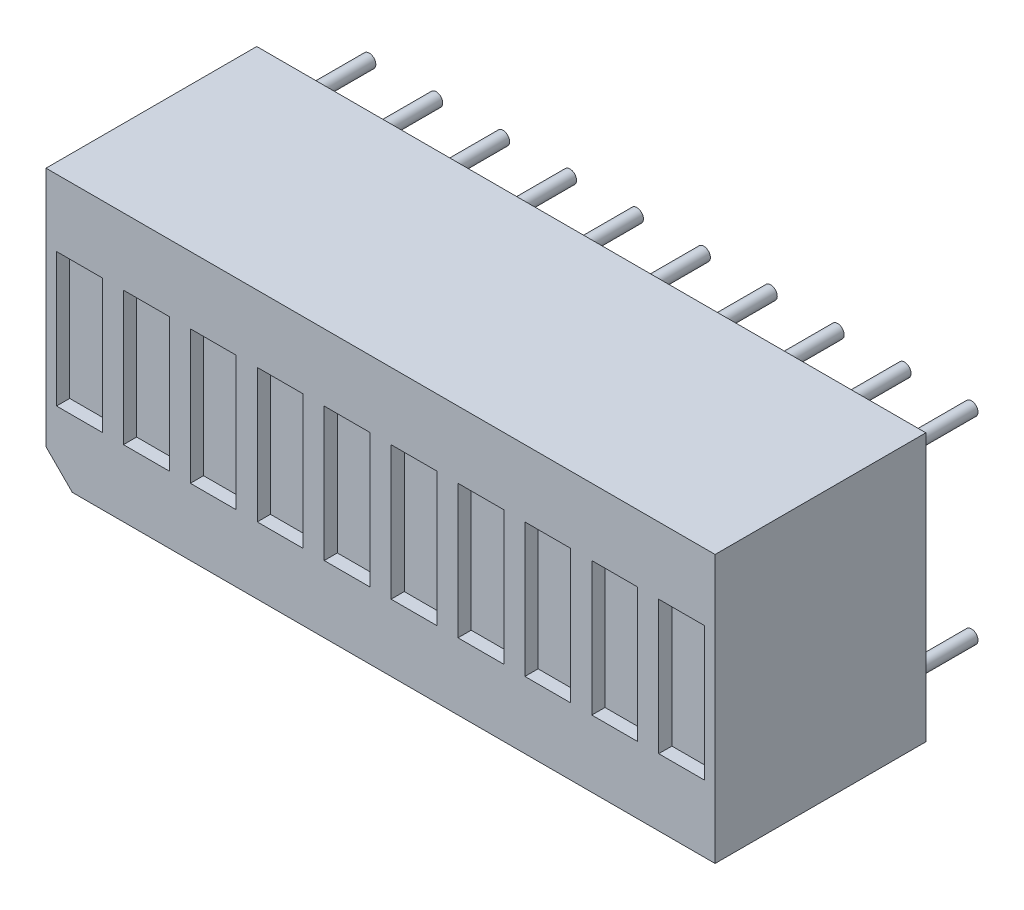
SolidWorks part; units mm, degrees
ref_plane "Alzado" through (0, 0, 0) normal (0, 0, 1) x (1, 0, 0)
ref_plane "Planta" through (0, 0, 0) normal (0, 1, 0) x (1, 0, 0)
ref_plane "Vista lateral" through (0, 0, 0) normal (1, 0, 0) x (0, 0, -1)
sketch "Croquis1" plane through (0, 0, 0) normal (0, 0, 1) x (1, 0, 0)
  line L0 (-11.7, -5.08) -> (-12.7, -4.08)
  line L1 (12.7, -5.08) -> (-11.7, -5.08)
  line L2 (12.7, -5.08) -> (12.7, 5.08)
  line L3 (12.7, 5.08) -> (-12.7, 5.08)
  line L4 (-12.7, -4.08) -> (-12.7, 5.08)
  line L5 (12.7, -5.08) -> (-12.7, 5.08) construction
  line L6 (12.7, 5.08) -> (-12.7, -5.08) construction
  point P0 (0, 0)
  dimension "D1" = 10.16
  dimension "D2" = 25.4
  dimension "D5" = 1
extrude "Saliente-Extruir1" add sketch "Croquis1" along normal blind 8
sketch "Croquis2" plane through (0, 0, 0) normal (0, 0, -1) x (-1, 0, 0)
  line L0 (0, 0) -> (-12.7, 0) construction
  line L1 (-12.7, -5.08) -> (-12.7, 5.08) construction
  line L3 (-12.7, 5.08) -> (12.7, 5.08) construction
  line L4 (0, 5.08) -> (0, 0) construction
  point P5 (-11.43, 3.75)
  point P9 (-8.89, 3.75)
  point P10 (-6.35, 3.75)
  point P11 (-1.27, 3.75)
  point P12 (-3.81, 3.75)
  dimension "D1" = 1.27
  dimension "D2" = 3.75
  dimension "D3" = 2.54
  dimension "D4" = 2.54
  dimension "D5" = 2.54
  dimension "D6" = 2.54
sketch "Croquis3" plane through (0, 0, 0) normal (0, 0, -1) x (-1, 0, 0)
  circle A0 centre (-11.43, 3.75) radius 0.25
  circle A1 centre (-8.89, 3.75) radius 0.25
  circle A2 centre (-6.35, 3.75) radius 0.25
  circle A3 centre (-3.81, 3.75) radius 0.25
  circle A4 centre (-1.27, 3.75) radius 0.25
  dimension "D1" = 0.5
extrude "Saliente-Extruir2" add sketch "Croquis3" along normal blind 3
pattern_linear "MatrizL1" count 2 spacing 12.7 along (-1, 0, 0) count 2 spacing 7.5 along (0, -1, 0) of "Saliente-Extruir2"
sketch "Croquis4" plane through (0, 0, 8) normal (0, 0, 1) x (1, 0, 0)
  line L0 (0, 0) -> (12.7, 0) construction
  line L1 (12.3, -2.54) -> (10.56, -2.54)
  line L2 (12.3, -2.54) -> (12.3, 2.54)
  line L3 (12.3, 2.54) -> (10.56, 2.54)
  line L4 (10.56, -2.54) -> (10.56, 2.54)
  line L5 (12.3, -2.54) -> (10.56, 2.54) construction
  line L6 (12.3, 2.54) -> (10.56, -2.54) construction
  line L7 (11.43, 0) -> (11.43, 3.75) construction
  point P0 (11.43, 0)
  dimension "D1" = 5.08
  dimension "D2" = 1.74
extrude "Cortar-Extruir1" cut sketch "Croquis4" against normal blind 0.5
pattern_linear "MatrizL2" count 10 spacing 2.54 along (-1, 0, 0) of "Cortar-Extruir1"
